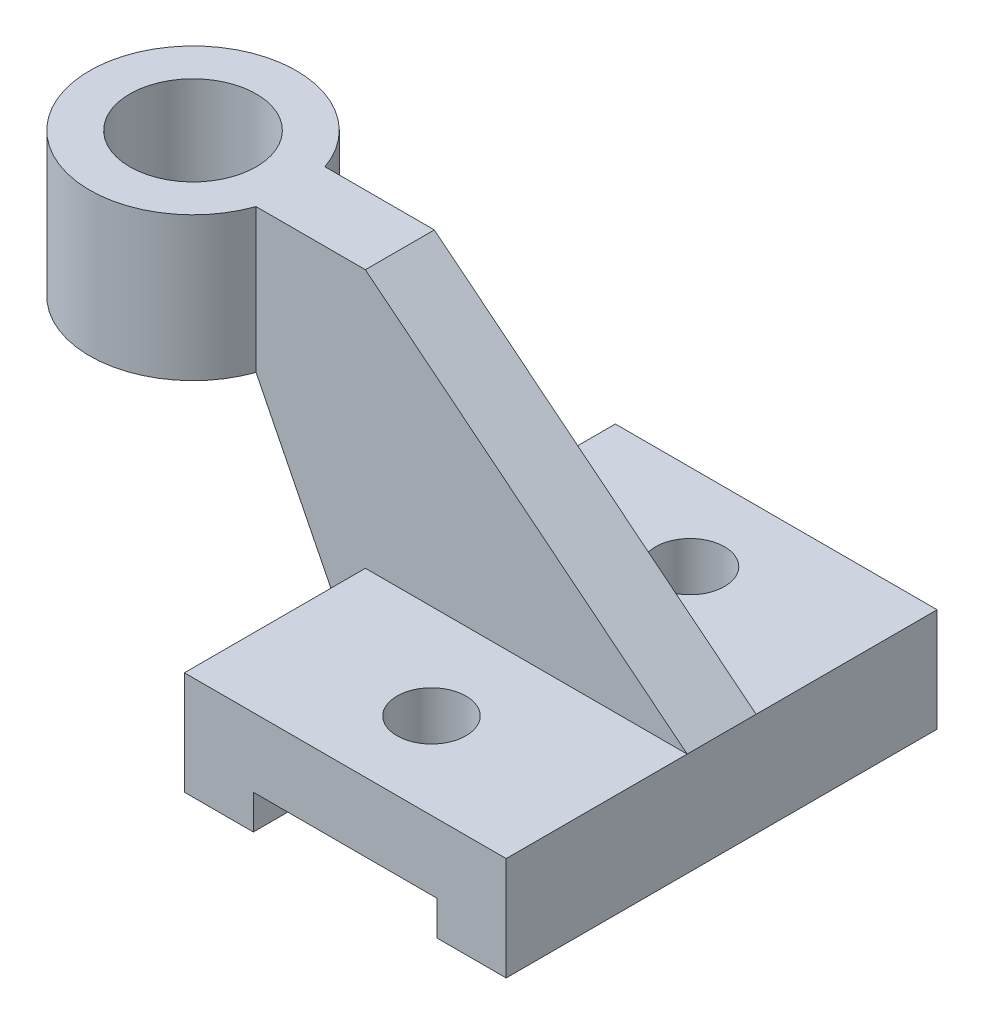
SolidWorks part; units mm, degrees
ref_plane "Front Plane" through (0, 0, 0) normal (0, 0, 1) x (1, 0, 0)
ref_plane "Top Plane" through (0, 0, 0) normal (0, 1, 0) x (1, 0, 0)
ref_plane "Right Plane" through (0, 0, 0) normal (1, 0, 0) x (0, 0, -1)
sketch "Sketch2" plane through (0, 0, 0) normal (0, 1, 0) x (1, 0, 0)
  line L1 (0, 0) -> (56, 0)
  line L2 (0, 0) -> (0, 75)
  line L3 (0, 75) -> (56, 75)
  line L4 (56, 0) -> (56, 75)
extrude "Boss-Extrude1" add sketch "Sketch2" along normal blind 18
sketch "Sketch3" plane through (0, 0, 0) normal (0, -1, 0) x (1, 0, 0)
  line L0 (0, 0) -> (12, 0)
  line L1 (0, 0) -> (56, 0) construction
  line L2 (12, 0) -> (44, 0)
  line L3 (44, 0) -> (44, -75)
  line L4 (56, -75) -> (0, -75) construction
  line L5 (44, -75) -> (12, -75)
  line L6 (12, -75) -> (12, 0)
extrude "Cut-Extrude1" cut sketch "Sketch3" against normal blind 6 contours L2 L3 L5 L6
sketch "Sketch5" plane through (0, 0, 0) normal (-1, 0, 0) x (0, 0, 1)
  line L0 (-37.5, 18) -> (-37.5, 81)
  line L1 (-75, 18) -> (0, 18) construction
  line L2 (-37.5, 81) -> (-37.5, 18)
sketch "Sketch6" plane through (0, 18, 0) normal (0, 1, 0) x (1, 0, 0)
  line L0 (0, 75) -> (0, 0) construction
  line L2 (-56, 60) -> (-56, 15)
  line L4 (56, 60) -> (56, 15)
  line L7 (56, 0) -> (56, 75) construction
  circle A0 centre (28, 15) radius 6
  circle A1 centre (28, 60) radius 6
  point P0 (0, 37.5)
extrude "Cut-Extrude2" cut sketch "Sketch6" against normal blind 47 contours A0 | A1
sketch "Sketch7" plane through (0, 18, 0) normal (0, 1, 0) x (1, 0, 0)
  line L0 (0, 75) -> (0, 0) construction
  line L1 (0, 37.5) -> (56, 37.5)
  line L2 (0, 37.5) -> (0, 43.5)
  line L3 (0, 43.5) -> (56, 43.5)
  line L4 (56, 37.5) -> (56, 43.5)
  line L5 (56, 0) -> (56, 75) construction
  line L7 (0, 37.5) -> (56, 37.5)
  line L8 (0, 37.5) -> (0, 31.5)
  line L9 (0, 31.5) -> (56, 31.5)
  line L10 (56, 37.5) -> (56, 31.5)
  line M11 (0, 75) -> (0, 0)
  line M13 (56, 0) -> (56, 75)
extrude "Boss-Extrude2" add sketch "Sketch7" along normal blind 45 contours L9 L1 M11 M13
sketch "Sketch8" plane through (0, 0, -43.5) normal (0, 0, -1) x (-1, 0, 0)
  line L0 (-56, 18) -> (0, 63)
  line L1 (0, 63) -> (-56, 63)
  line L2 (-56, 63) -> (-56, 18)
extrude "Cut-Extrude3" cut sketch "Sketch8" against normal blind 45
sketch "Sketch9" plane through (0, 0, -43.5) normal (0, 0, -1) x (-1, 0, 0)
  line L1 (0, 63) -> (36, 63)
  line L2 (0, 63) -> (0, 38)
  line L3 (0, 38) -> (36, 38)
  line L4 (36, 63) -> (36, 38)
  dimension "D1" = 36
extrude "Boss-Extrude5" add sketch "Sketch9" against normal blind 12 contours L2 L1 L4 L3
sketch "Sketch10" plane through (0, 63, 0) normal (0, 1, 0) x (1, 0, 0)
  line L0 (-36, 31.5) -> (-36, 43.5) construction
  circle A0 centre (-36, 37.5) radius 18
  dimension "D1" = 36
extrude "Boss-Extrude9" add sketch "Sketch10" against normal blind 25
sketch "Sketch11" plane through (0, 63, 0) normal (0, 1, 0) x (1, 0, 0)
  circle A0 centre (-36, 37.5) radius 11
  dimension "D1" = 22
extrude "Cut-Extrude4" cut sketch "Sketch11" against normal blind 25
sketch "Sketch12" plane through (0, 0, -43.5) normal (0, 0, -1) x (-1, 0, 0)
  line L0 (19.0294, 38) -> (0, 0)
  line L1 (0, 0) -> (0, 38)
  line L2 (0, 38) -> (19.0294, 38)
extrude "Boss-Extrude10" add sketch "Sketch12" against normal blind 12
